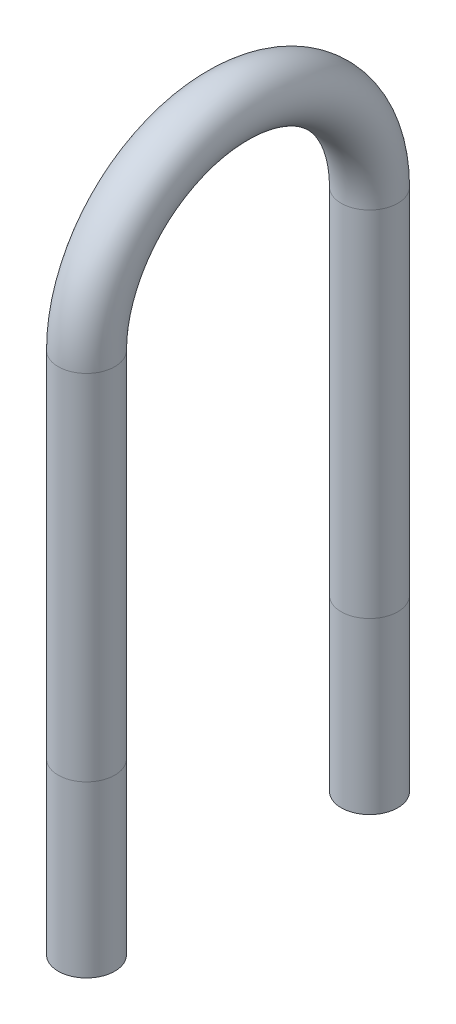
SolidWorks part; units mm, degrees
material "AISI 1020 Steel, Cold Rolled"
ref_plane "Front Plane" through (0, 0, 0) normal (0, 0, 1) x (1, 0, 0)
ref_plane "Top Plane" through (0, 0, 0) normal (0, 1, 0) x (1, 0, 0)
ref_plane "Right Plane" through (0, 0, 0) normal (1, 0, 0) x (0, 0, -1)
sketch "Sketch1" plane through (0, 0, 0) normal (1, 0, 0) x (0, 0, -1)
  line L0 (0, 0) -> (0, 317.5)
  line L1 (254, 0) -> (254, 317.5)
  line L2 (0, 0) -> (0, -152.4)
  line L3 (254, 0) -> (254, -152.4)
  arc A0 (254, 317.5) -> (0, 317.5) centre (127, 317.5) ccw
  dimension "D2" = 127
  dimension "D1" = 317.5
  dimension "D3" = 152.4
ref_plane "Plane1" through (0, -152.4, 0) normal (0, 1, 0) x (1, 0, 0)
sketch "Sketch2" plane through (0, -152.4, 0) normal (0, 1, 0) x (1, 0, 0)
  circle A0 centre (0, 0) radius 25.4
  circle A1 centre (0, 0) radius 23.749
  dimension "D1" = 50.8
  dimension "D2" = 1.651
sweep "Sweep1" add profiles "Sketch2" path "Sketch1"
